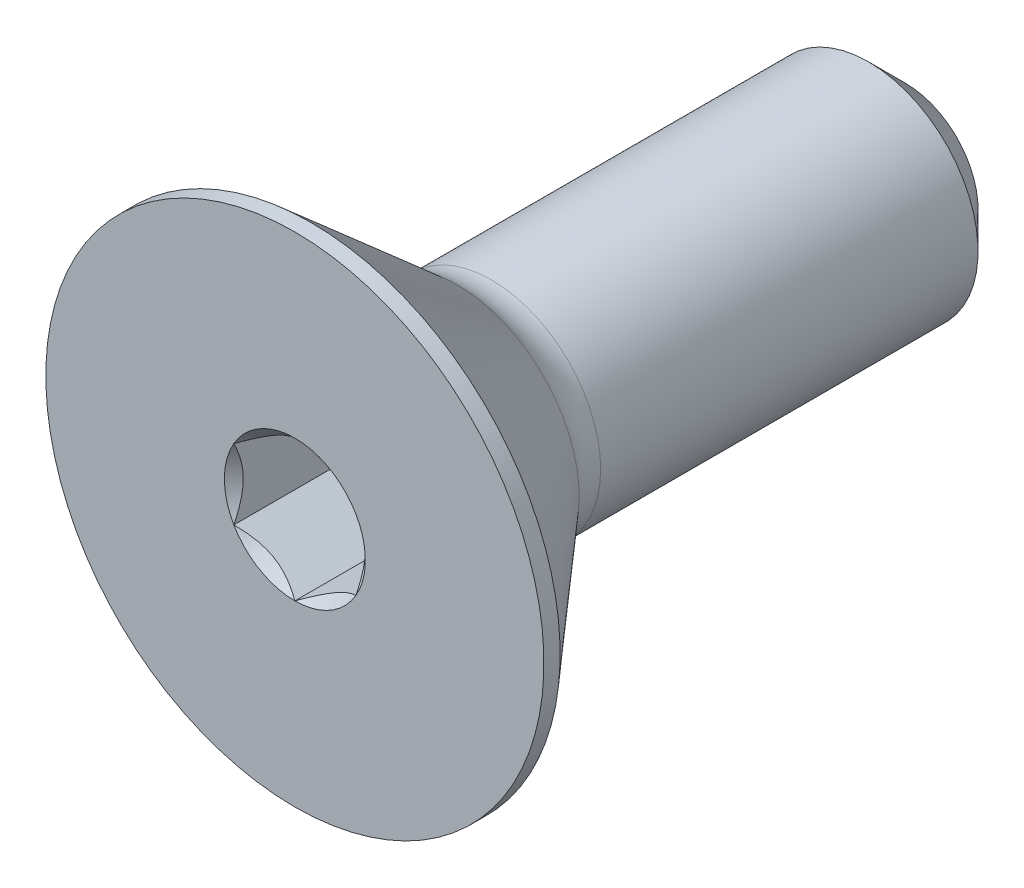
SolidWorks part; units mm, degrees
ref_plane "Front" through (0, 0, 0) normal (0, 0, 1) x (1, 0, 0)
ref_plane "Top" through (0, 0, 0) normal (0, 1, 0) x (1, 0, 0)
ref_plane "Right" through (0, 0, 0) normal (1, 0, 0) x (0, 0, -1)
sketch "Sketch1" plane through (0, 0, 0) normal (1, 0, 0) x (0, 0, -1)
  line L0 (0, 3.2385) -> (0.2108, 3.2385) construction
  line L1 (0.2108, 3.2385) -> (2.1082, 1.5891) construction
  line L2 (0, 1.4224) -> (7.9375, 1.4224)
  line L3 (7.9375, 1.4224) -> (7.9375, 0)
  line L4 (7.9375, 0) -> (0, 0)
  line L5 (0, 0) -> (0, 3.2385) construction
  line L6 (0, 3.2385) -> (0, -3.2385) construction
  line L7 (7.9375, 1.4224) -> (7.9375, -1.4224) construction
  line L8 (0, -3.2385) -> (0.2108, -3.2385) construction
  line L9 (0.2108, -3.2385) -> (2.1082, -1.5891) construction
  line L11 (0, 1.4224) -> (0, 0)
  line L12 (2.5541, 1.4224) -> (2.5541, 0) construction
  arc A1 (2.1082, 1.5891) -> (2.5541, 1.4224) centre (2.5541, 2.1021) ccw construction
  dimension "D1" = 0.2108
revolve "Revolve1" add sketch "Sketch1" angle 360 mid plane about L4
sketch "Sketch3" plane through (0, 0, -7.9375) normal (0, 0, -1) x (-1, 0, 0)
  circle A0 centre (0, 0) radius 1.4224
sketch "Sketch2" plane through (0, 0, 0) normal (1, 0, 0) x (0, 0, -1)
  line L0 (7.9375, 1.4224) -> (8.4931, 1.4224)
  line L1 (8.4931, 1.4224) -> (8.255, 1.01)
  line L2 (8.255, 1.01) -> (8.1756, 1.01)
  line L3 (8.1756, 1.01) -> (7.9375, 1.4224)
  line L4 (8.0566, 1.2162) -> (8.3741, 1.2162) construction
  dimension "D1" = 60
  dimension "D2" = 0.0794
  dimension "D3" = 0.3175
chamfer "Chamfer1" distance 0.4763 angle 45 1 edges at (0, 1.4224, -7.9375)
sketch "Sketch7" plane through (0, 0, 0) normal (1, 0, 0) x (0, 0, -1)
  line L0 (0, 3.2385) -> (0.2108, 3.2385) construction
  line L1 (0.2108, 3.2385) -> (2.1082, 1.5891) construction
  line L2 (0, 3.2385) -> (0.2108, 3.2385)
  line L3 (0.2108, 3.2385) -> (2.1082, 1.5891)
  line L4 (2.5541, 1.4224) -> (2.5541, 0) construction
  line L5 (2.5541, 1.4224) -> (2.5541, 0)
  line L7 (0, 0) -> (0, 3.2385) construction
  line L8 (0, 0) -> (0, 3.2385)
  line L9 (0, 0) -> (2.5541, 0)
  line L10 (3.5623, 0) -> (-3.5623, 0) construction
  arc A0 (2.1082, 1.5891) -> (2.5541, 1.4224) centre (2.5541, 2.1021) ccw construction
  arc A1 (2.1082, 1.5891) -> (2.5541, 1.4224) centre (2.5541, 2.1021) ccw
revolve "Revolve2" add sketch "Sketch7" angle 360 mid plane about L9
ref_plane "Plane1" through (0, 0, -2.5541) normal (0, 0, 1) x (1, 0, 0)
sketch "Sketch8" plane through (0, 0, -2.5541) normal (0, 0, 1) x (1, 0, 0)
  circle A0 centre (0, 0) radius 1.4224
extrude "Boss-Extrude1" add sketch "Sketch8" against normal through all draft 45
sketch "Sketch11" [suppressed] plane through (0, 0, 0) normal (1, 0, 0) x (0, 0, -1)
  line L0 (4.4996, 0) -> (-4.4996, 0) construction
  line L1 (7.3025, 3.8989) -> (1.7272, 3.8989)
  line L2 (7.3025, 3.8989) -> (7.3025, -3.8989)
  line L3 (7.3025, -3.8989) -> (1.7272, -3.8989)
  line L4 (1.7272, 3.8989) -> (1.7272, -3.8989)
  line L5 (0, 3.8989) -> (0.1727, 3.8989) construction
  line L7 (4.7625, 1.7526) -> (4.7625, 0) construction
  point P4 (1.7272, 0)
  dimension "D1" = 2.54
extrude "Cut-Extrude4" [suppressed] cut sketch "Sketch11" against normal through all and the other way through all
combine bodies "Combine1" operation type add bodies to combine 117 108
sketch "Sketch5" plane through (0, 0, 0) normal (0, 0, 1) x (1, 0, 0)
  line L1 (0.7937, -0.4583) -> (0.7937, 0.4583)
  line L2 (0.7937, 0.4583) -> (0, 0.9165)
  line L3 (0, 0.9165) -> (-0.7938, 0.4583)
  line L4 (-0.7938, 0.4583) -> (-0.7938, -0.4583)
  line L5 (-0.7938, -0.4583) -> (0, -0.9165)
  line L6 (0, -0.9165) -> (0.7937, -0.4583)
  circle A0 centre (0, 0) radius 0.7937 construction
  dimension "Hex" = 1.5875
extrude "Cut-Extrude2" cut sketch "Sketch5" against normal blind 1.4757
sketch "Sketch6" plane through (0, 0, 0) normal (0, 0, 1) x (1, 0, 0)
  circle A0 centre (0, 0) radius 0.9165
extrude "Cut-Extrude3" cut sketch "Sketch6" against normal blind 1.4757 draft 45
sketch "Sketch9" [suppressed] plane through (0, 0, -12.3809) normal (0, 0, 1) x (1, 0, 0)
  circle A1 centre (0, 0) radius 9.525
  circle A2 centre (0, 0) radius 9.525
  point P0 (0, 9.525)
  dimension "D1" = 0
extrude "Boss-Extrude2" [suppressed] add sketch "Sketch9" against normal offset from surface (44.7691 mm away) 44.45
sketch "Sketch10" plane through (0, 0, 0) normal (1, 0, 0) x (0, 0, -1)
  line L0 (7.9375, 1.4224) -> (7.9375, -1.4224) construction
  point P0 (6.985, -1.4224)
  dimension "D1" = 0.9525
equation "\"D3@Helix/Spiral1\" = \"Lg@Sketch1\""
equation "\"D2@Sketch2\" = \"D4@Helix/Spiral1\" * .125"
equation "\"D3@Sketch2\" = \"D4@Helix/Spiral1\" * .5"
equation "\"D1@Chamfer1\" = \"D4@Helix/Spiral1\" * .75"
equation "\"D1@Cut-Extrude2\" = \"Head Ht@Sketch1\" * .7"
equation "\"D1@Sketch1\" = \"Head Ht@Sketch1\" * .1"
equation "\"D1@Sketch10\" = \"D4@Helix/Spiral1\" * 1.5"
equation "\"D1@Cut-Extrude3\" = \"D1@Cut-Extrude2\""
